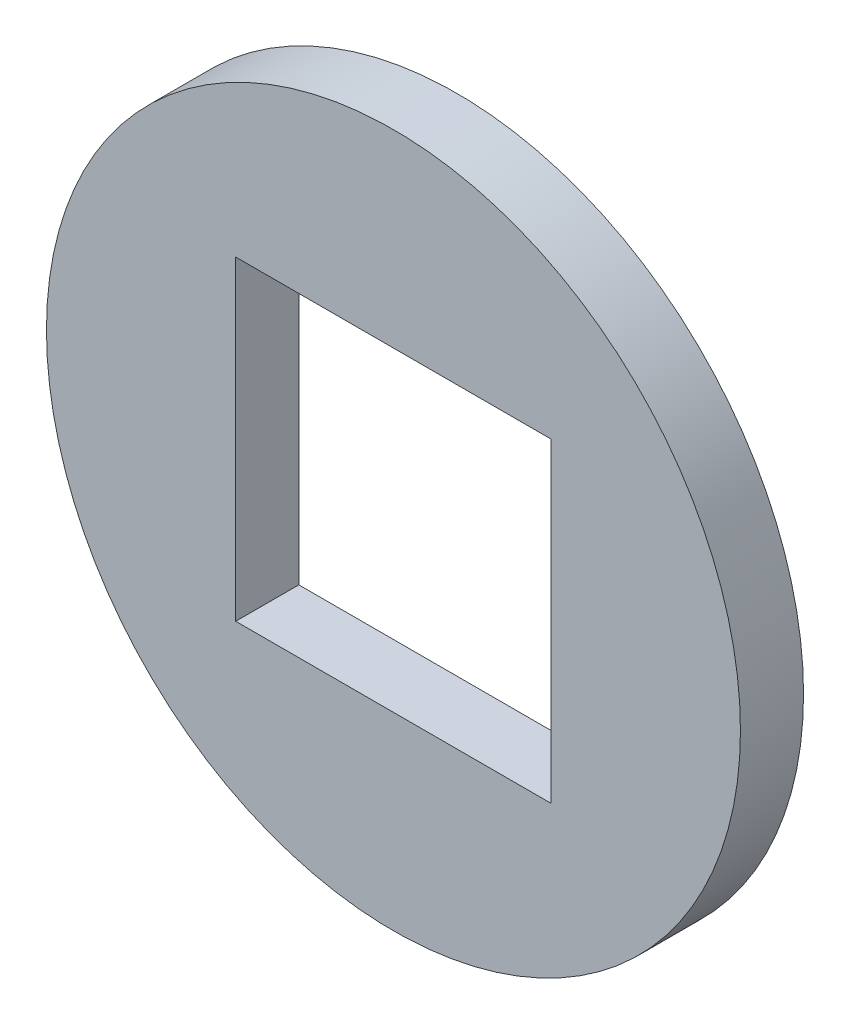
SolidWorks part; units mm, degrees
material "Acrylic (Medium-high impact)"
ref_plane "Front Plane" through (0, 0, 0) normal (0, 0, 1) x (1, 0, 0)
ref_plane "Top Plane" through (0, 0, 0) normal (0, 1, 0) x (1, 0, 0)
ref_plane "Right Plane" through (0, 0, 0) normal (1, 0, 0) x (0, 0, -1)
sketch "Sketch1" plane through (0, 0, 0) normal (0, 0, 1) x (1, 0, 0)
  line L1 (-5, -5) -> (5, -5)
  line L2 (-5, -5) -> (-5, 5)
  line L3 (-5, 5) -> (5, 5)
  line L4 (5, -5) -> (5, 5)
  line L5 (-5, -5) -> (5, 5) construction
  line L6 (-5, 5) -> (5, -5) construction
  circle A0 centre (0, 0) radius 11
  dimension "D1" = 22
  dimension "D2" = 10
  dimension "D3" = 10
extrude "Boss-Extrude1" add sketch "Sketch1" along normal blind 2
